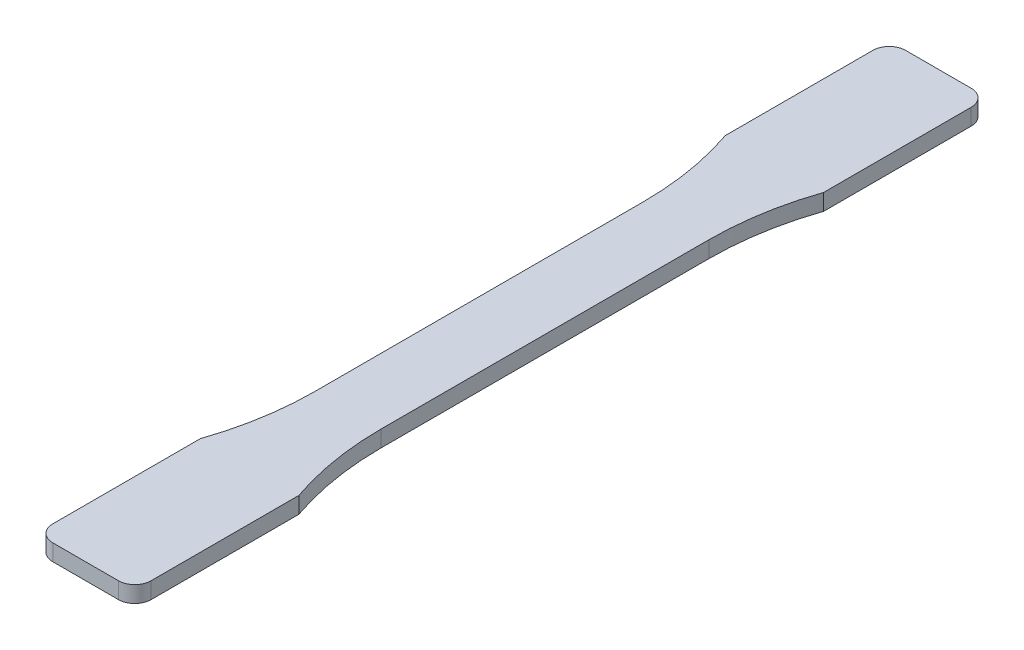
SolidWorks part; units mm, degrees
ref_plane "Front Plane" through (0, 0, 0) normal (0, 0, 1) x (1, 0, 0)
ref_plane "Top Plane" through (0, 0, 0) normal (0, 1, 0) x (1, 0, 0)
ref_plane "Right Plane" through (0, 0, 0) normal (1, 0, 0) x (0, 0, -1)
sketch "Sketch1" plane through (0, 0, 0) normal (0, 1, 0) x (1, 0, 0)
  line L0 (6.35, 31.75) -> (6.35, -31.75)
  line L1 (-9.525, 82.55) -> (9.525, 82.55)
  line L2 (-9.525, 82.55) -> (-9.525, 50.8)
  line L3 (-9.525, -82.55) -> (9.525, -82.55)
  line L4 (9.525, 82.55) -> (9.525, 50.8)
  line L5 (-9.525, 82.55) -> (9.525, -82.55) construction
  line L6 (-9.525, -82.55) -> (9.525, 82.55) construction
  line L7 (9.525, -50.8) -> (9.525, -82.55)
  line L8 (-6.35, 31.75) -> (-6.35, -31.75)
  line L9 (-9.525, -50.8) -> (-9.525, -82.55)
  arc A0 (6.35, 31.75) -> (9.525, 50.8) centre (65.0875, 31.75) cw
  arc A1 (6.35, -31.75) -> (9.525, -50.8) centre (65.0875, -31.75) ccw
  arc A2 (-6.35, -31.75) -> (-9.525, -50.8) centre (-65.0875, -31.75) cw
  arc A3 (-6.35, 31.75) -> (-9.525, 50.8) centre (-65.0875, 31.75) ccw
  point P0 (0, 0)
  point P18 (0, 0)
  point P19 (0, 0)
  point P20 (0, 0)
  point P21 (0, 0)
  dimension "D1" = 19.05
  dimension "D2" = 165.1
  dimension "D3" = 31.75
  dimension "D4" = 19.05
  dimension "D5" = 31.75
  dimension "D6" = 19.05
  dimension "D7" = 3.175
  dimension "D8" = 3.175
extrude "Boss-Extrude1" add sketch "Sketch1" along normal mid plane 3.175
fillet "Fillet1" radius 3.175 4 edges at (-9.525, 0, -82.55) (9.525, 0, -82.55) (-9.525, 0, 82.55) (9.525, 0, 82.55)
